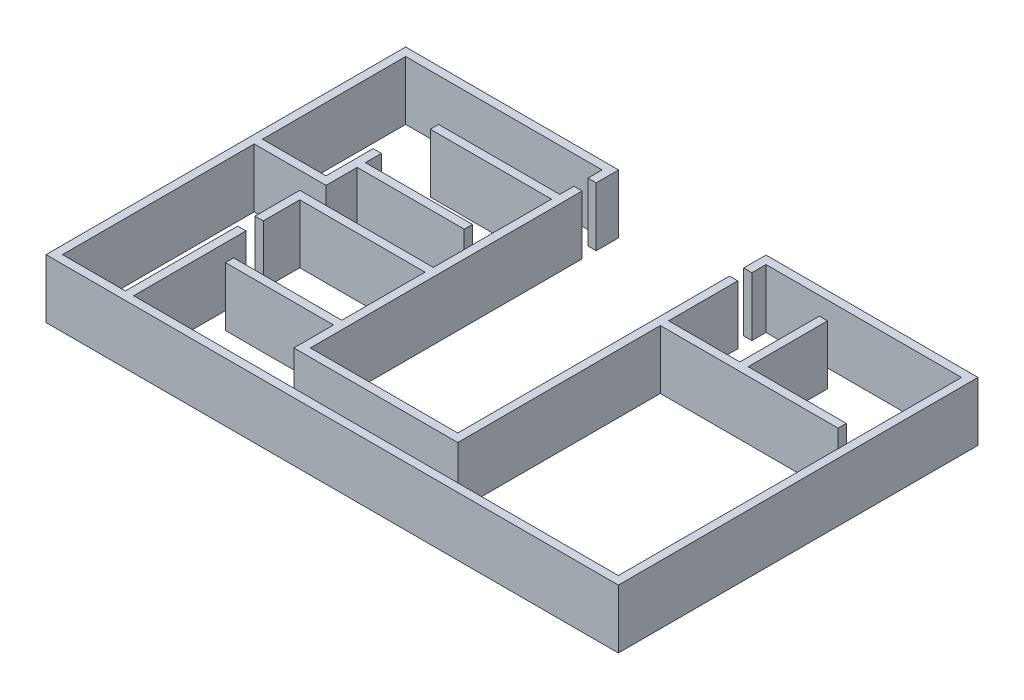
SolidWorks part; units mm, degrees
ref_plane "Front Plane" through (0, 0, 0) normal (0, 0, 1) x (1, 0, 0)
ref_plane "Top Plane" through (0, 0, 0) normal (0, 1, 0) x (1, 0, 0)
ref_plane "Right Plane" through (0, 0, 0) normal (1, 0, 0) x (0, 0, -1)
sketch "hyperport_plan" plane through (0, 0, 0) normal (0, 1, 0) x (1, 0, 0)
  line L0 (-6225, 15285) -> (-24325, 15285)
  line L1 (-24325, 15285) -> (-24325, -15285)
  line L2 (-24325, -15285) -> (24325, -15285)
  line L3 (24325, -15285) -> (24325, 15285)
  line L4 (24325, 15285) -> (6305, 15285)
  line L5 (6305, 15285) -> (6305, 13385)
  line L6 (6305, 13385) -> (7005, 13385)
  line L7 (7005, 13385) -> (7005, 14585)
  line L8 (7005, 14585) -> (23625, 14585)
  line L9 (23625, 14585) -> (23625, -14585)
  line L10 (23625, -14585) -> (-17575, -14585)
  line L11 (-17575, -14585) -> (-17575, -5035)
  line L12 (-17575, -5035) -> (-18275, -5035)
  line L13 (-18275, -5035) -> (-18275, -14585)
  line L14 (-18275, -14585) -> (-23625, -14585)
  line L15 (-23625, -14585) -> (-23625, 1715)
  line L16 (-23625, 1715) -> (-17525, 1715)
  line L17 (-17525, 1715) -> (-17525, 4365)
  line L18 (-17525, 4365) -> (-8425, 4365)
  line L19 (-8425, 4365) -> (-8425, 5065)
  line L20 (-8425, 5065) -> (-17525, 5065)
  line L21 (-17525, 5065) -> (-17525, 6425)
  line L22 (-17525, 6425) -> (-18225, 6425)
  line L23 (-18225, 6425) -> (-18225, 2415)
  line L24 (-18225, 2415) -> (-23625, 2415)
  line L25 (-23625, 2415) -> (-23625, 14585)
  line L26 (-23625, 14585) -> (-6925, 14585)
  line L27 (-6925, 14585) -> (-6925, 13385)
  line L28 (-6925, 13385) -> (-6225, 13385)
  line L29 (-6225, 13385) -> (-6225, 15285)
  line L30 (-6225, 12185) -> (-6225, 10985)
  line L31 (-6225, 12185) -> (-6925, 12185)
  line L32 (-6925, 12185) -> (-6925, 10985)
  line L33 (-6925, 10985) -> (-17225, 10985)
  line L34 (-17225, 10985) -> (-17225, 10285)
  line L35 (-17225, 10285) -> (-6925, 10285)
  line L36 (-6925, 10285) -> (-6925, 235)
  line L37 (-6925, 235) -> (-18275, 235)
  line L38 (-18275, 235) -> (-18275, -3565)
  line L39 (-18275, -3565) -> (-17575, -3565)
  line L40 (-17575, -3565) -> (-17575, -465)
  line L41 (-17575, -465) -> (-6925, -465)
  line L42 (-6925, -465) -> (-6925, -7545)
  line L43 (-6925, -7545) -> (-16115, -7545)
  line L44 (-16115, -7545) -> (-16115, -8245)
  line L45 (-16115, -8245) -> (-6925, -8245)
  line L46 (-6925, -8245) -> (-6925, -11615)
  line L47 (-6925, -11615) -> (7005, -11615)
  line L48 (7005, -11615) -> (7005, 5605)
  line L49 (7005, 5605) -> (22115, 5605)
  line L50 (22115, 5605) -> (22115, 6305)
  line L51 (22115, 6305) -> (13765, 6305)
  line L52 (13765, 6305) -> (13765, 13055)
  line L53 (13765, 13055) -> (13065, 13055)
  line L54 (13065, 13055) -> (13065, 6305)
  line L55 (13065, 6305) -> (7005, 6305)
  line L56 (7005, 6305) -> (7005, 12185)
  line L57 (7005, 12185) -> (6305, 12185)
  line L58 (6305, 12185) -> (6305, -10915)
  line L59 (6305, -10915) -> (-6225, -10915)
  line L60 (-6225, -10915) -> (-6225, 10985)
  dimension "D1" = 18100
  dimension "D2" = 30570
  dimension "D3" = 48650
  dimension "D4" = 41200
  dimension "D5" = 29170
  dimension "D6" = 16620
  dimension "D7" = 9550
  dimension "D8" = 16300
  dimension "D9" = 6100
  dimension "D10" = 1200
extrude "walls_5m" add sketch "hyperport_plan" along normal blind 5000
